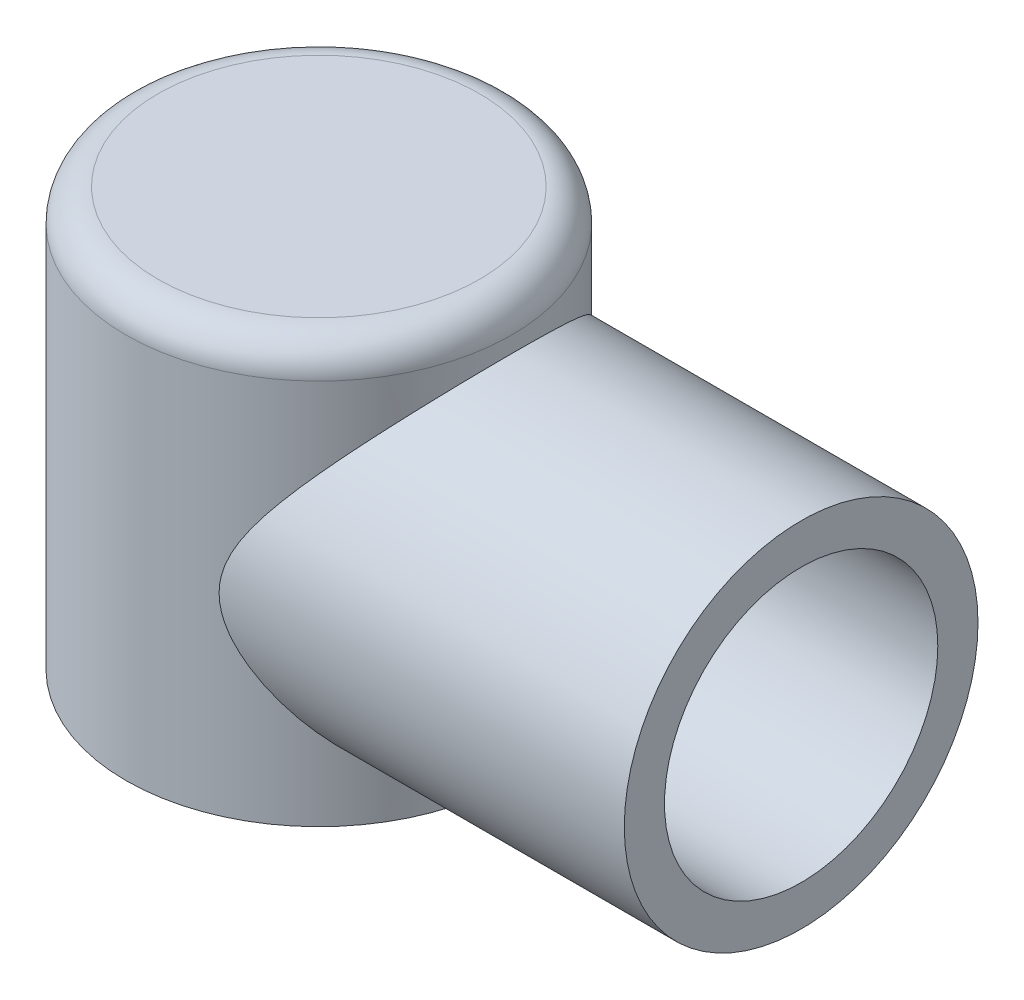
SolidWorks part; units mm, degrees
ref_plane "Front Plane" through (0, 0, 0) normal (0, 0, 1) x (1, 0, 0)
ref_plane "Top Plane" through (0, 0, 0) normal (0, 1, 0) x (1, 0, 0)
ref_plane "Right Plane" through (0, 0, 0) normal (1, 0, 0) x (0, 0, -1)
sketch "Sketch1" plane through (0, 0, 0) normal (0, 1, 0) x (1, 0, 0)
  circle A0 centre (0, 0) radius 60
  dimension "D1" = 120
extrude "Boss-Extrude1" add sketch "Sketch1" along normal blind 130
fillet "Fillet1" radius 10 1 edges at (0, 130, 60)
sketch "Sketch2" plane through (0, 0, 0) normal (1, 0, 0) x (0, 0, -1)
  circle A0 centre (0, 60) radius 55
  dimension "D1" = 110
extrude "Boss-Extrude2" add sketch "Sketch2" along normal blind 150
sketch "Sketch3" plane through (0, 0, 0) normal (1, 0, 0) x (0, 0, -1)
  circle A0 centre (0, 60) radius 42.5
  dimension "D1" = 85
extrude "Cut-Extrude1" cut sketch "Sketch3" along normal blind 150 contours A0
